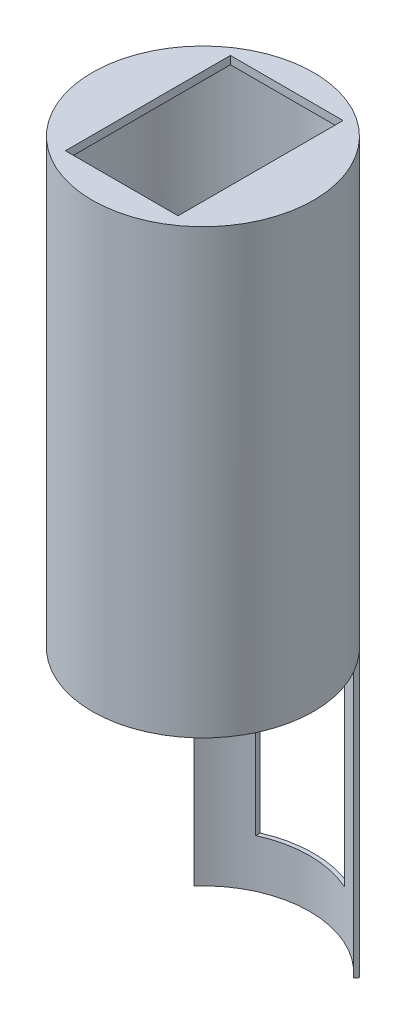
SolidWorks part; units mm, degrees
ref_plane "前基準面" through (0, 0, 0) normal (0, 0, 1) x (1, 0, 0)
ref_plane "上基準面" through (0, 0, 0) normal (0, 1, 0) x (1, 0, 0)
ref_plane "右基準面" through (0, 0, 0) normal (1, 0, 0) x (0, 0, -1)
sketch "草圖1" plane through (0, 0, 0) normal (0, 1, 0) x (1, 0, 0)
  circle A0 centre (0, 0) radius 27.5
  circle A1 centre (0, 0) radius 26.5
  dimension "D1" = 55
  dimension "D2" = 53
extrude "填料-伸長1" add sketch "草圖1" along normal blind 110 and the other way blind 70 contours A0
sketch "草圖2" plane through (0, 0, 0) normal (0, 1, 0) x (1, 0, 0)
  line L0 (0, 0) -> (0, 31.9988) construction
  circle A0 centre (0, 0) radius 26.5
  dimension "D1" = 53
extrude "除料-伸長1" cut sketch "草圖2" along normal blind 108 and the other way blind 70
sketch "草圖6" plane through (0, 0, 0) normal (0, 1, 0) x (1, 0, 0)
  line L0 (-26.5, 0) -> (26.3008, 0)
  line L1 (0, 0) -> (0, 27.8442) construction
  line L3 (26.3008, 0) -> (26.5, 0)
  line L5 (-20.4464, 18.3901) -> (-19.794, 17.6195)
  line L6 (20.4464, 18.3901) -> (19.794, 17.6195)
  arc A0 (-27.5, 0) -> (27.5, 0) centre (0, 0) ccw
  circle A1 centre (0, 0) radius 27.5 construction
  circle A3 centre (0, 0) radius 26.5 construction
  arc A6 (-27.5, 0) -> (-20.4464, 18.3901) centre (0, 0) cw
  arc A9 (-26.5, 0) -> (-19.794, 17.6195) centre (0, 0) cw
  circle A10 centre (0, 0) radius 26.5 construction
  arc A11 (27.5, 0) -> (20.4464, 18.3901) centre (0, 0) ccw
  arc A12 (26.5, 0) -> (19.794, 17.6195) centre (0, 0) ccw
extrude "除料-伸長6" cut sketch "草圖6" against normal blind 70
ref_plane "平面3" through (0, -10, 0) normal (0, 1, 0) x (1, 0, 0)
sketch "草圖7" plane through (0, -10, 0) normal (0, 1, 0) x (1, 0, 0)
  line L0 (0, 0) -> (0, 28.0951) construction
  line L1 (11, 17.9106) -> (-11, 17.9106)
  line L2 (-11, 17.9106) -> (-11, 37.9106)
  line L3 (-11, 37.9106) -> (11, 37.9106)
  line L4 (11, 17.9106) -> (11, 37.9106)
  point P8 (0, 37.9106)
  point P9 (0, 17.9106)
  dimension "D1" = 11
  dimension "D2" = 20
extrude "除料-伸長7" cut sketch "草圖7" against normal blind 48
sketch "草圖8" plane through (0, 0, 0) normal (0, 1, 0) x (1, 0, 0)
  line L0 (0, 27.5) -> (0, -27.5) construction
  line L1 (14, 20.8205) -> (-14, 20.8205)
  line L2 (-14, 20.8205) -> (-14, -20.1795)
  line L3 (-14, -20.1795) -> (14, -20.1795)
  line L4 (14, 20.8205) -> (14, -20.1795)
  circle A1 centre (0, 0) radius 27.5 construction
  point P11 (0, -20.1795)
  point P12 (0, 20.8205)
  dimension "D1" = 28
  dimension "D2" = 41
extrude "除料-伸長8" cut sketch "草圖8" along normal blind 119
